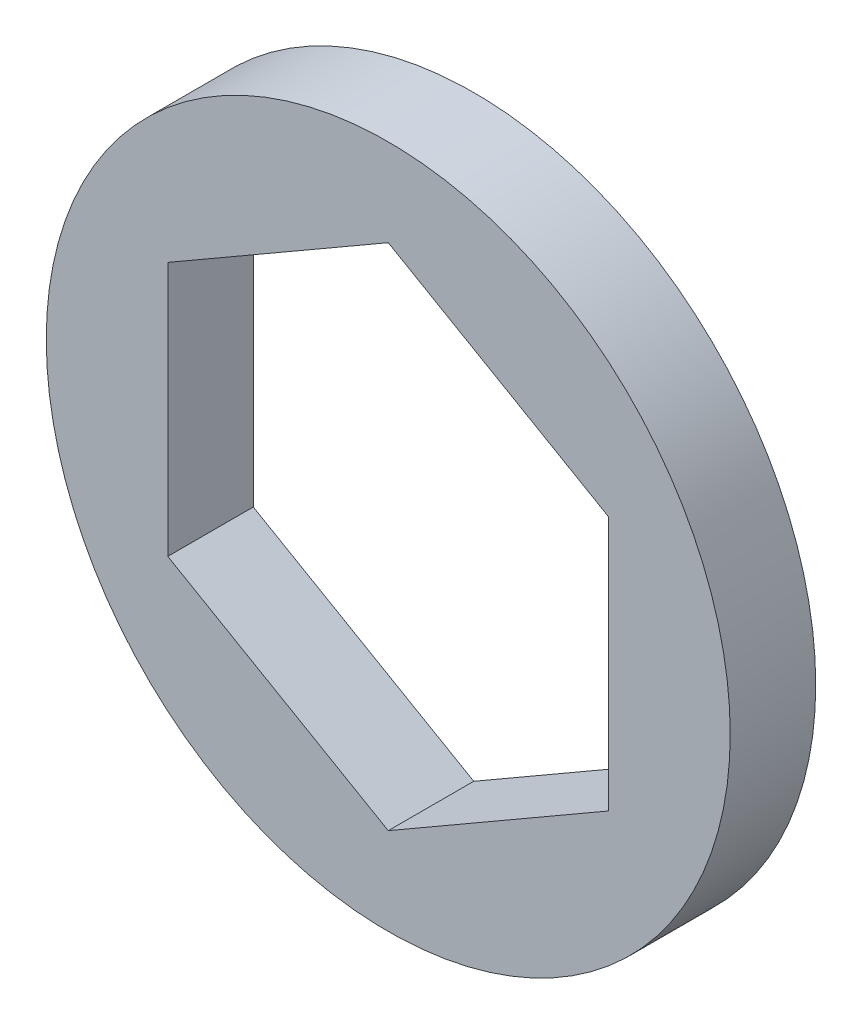
SolidWorks part; units mm, degrees
ref_plane "Front Plane" through (0, 0, 0) normal (0, 0, 1) x (1, 0, 0)
ref_plane "Top Plane" through (0, 0, 0) normal (0, 1, 0) x (1, 0, 0)
ref_plane "Right Plane" through (0, 0, 0) normal (1, 0, 0) x (0, 0, -1)
sketch "Sketch1" plane through (0, 0, 0) normal (0, 0, 1) x (1, 0, 0)
  line L1 (0, 7.5633) -> (-6.55, 3.7816)
  line L2 (-6.55, 3.7816) -> (-6.55, -3.7816)
  line L3 (-6.55, -3.7816) -> (0, -7.5633)
  line L4 (0, -7.5633) -> (6.55, -3.7816)
  line L5 (6.55, -3.7816) -> (6.55, 3.7816)
  line L6 (6.55, 3.7816) -> (0, 7.5633)
  circle A0 centre (0, 0) radius 6.55 construction
  circle A1 centre (0, 0) radius 10.16
  dimension "D1" = 20.32
extrude "Boss-Extrude1" add sketch "Sketch1" along normal blind 2.54
